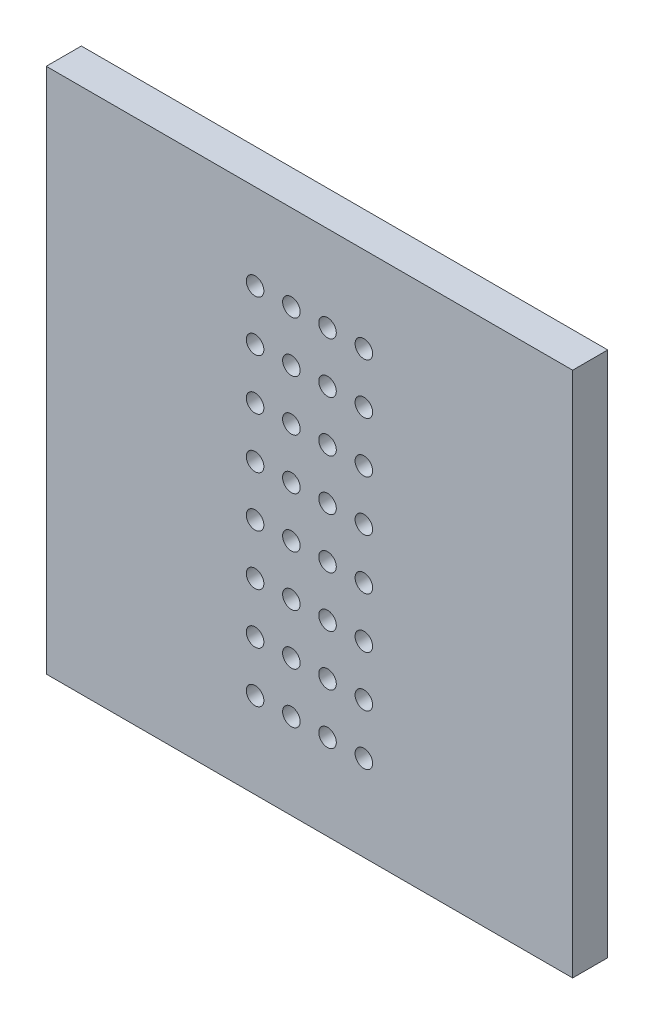
SolidWorks part; units mm, degrees
ref_plane "Plan de face" through (0, 0, 0) normal (0, 0, 1) x (1, 0, 0)
ref_plane "Plan de dessus" through (0, 0, 0) normal (0, 1, 0) x (1, 0, 0)
ref_plane "Plan de droite" through (0, 0, 0) normal (1, 0, 0) x (0, 0, -1)
sketch "Esquisse1" plane through (0, 0, 0) normal (0, 0, 1) x (1, 0, 0)
  line L1 (-15, -15) -> (15, -15)
  line L2 (-15, -15) -> (-15, 15)
  line L3 (-15, 15) -> (15, 15)
  line L4 (15, -15) -> (15, 15)
  line L5 (-15, -15) -> (15, 15) construction
  line L6 (-15, 15) -> (15, -15) construction
  point P0 (0, 0)
extrude "Base_Plate" add sketch "Esquisse1" along normal blind 2
sketch "Sketch_Perforations" plane through (0, 0, 2) normal (0, 0, 1) x (1, 0, 0)
  circle A0 centre (-3.1, -10.11) radius 0.5
  circle A1 centre (-3.1, -7.22) radius 0.5
  circle A2 centre (-3.1, -4.33) radius 0.5
  circle A3 centre (-3.1, -1.44) radius 0.5
  circle A4 centre (-3.1, 1.44) radius 0.5
  circle A5 centre (-3.1, 4.33) radius 0.5
  circle A6 centre (-3.1, 7.22) radius 0.5
  circle A7 centre (-3.1, 10.11) radius 0.5
  circle A8 centre (-1.03, -10.11) radius 0.5
  circle A9 centre (-1.03, -7.22) radius 0.5
  circle A10 centre (-1.03, -4.33) radius 0.5
  circle A11 centre (-1.03, -1.44) radius 0.5
  circle A12 centre (-1.03, 1.44) radius 0.5
  circle A13 centre (-1.03, 4.33) radius 0.5
  circle A14 centre (-1.03, 7.22) radius 0.5
  circle A15 centre (-1.03, 10.11) radius 0.5
  circle A16 centre (1.03, -10.11) radius 0.5
  circle A17 centre (1.03, -7.22) radius 0.5
  circle A18 centre (1.03, -4.33) radius 0.5
  circle A19 centre (1.03, -1.44) radius 0.5
  circle A20 centre (1.03, 1.44) radius 0.5
  circle A21 centre (1.03, 4.33) radius 0.5
  circle A22 centre (1.03, 7.22) radius 0.5
  circle A23 centre (1.03, 10.11) radius 0.5
  circle A24 centre (3.1, -10.11) radius 0.5
  circle A25 centre (3.1, -7.22) radius 0.5
  circle A26 centre (3.1, -4.33) radius 0.5
  circle A27 centre (3.1, -1.44) radius 0.5
  circle A28 centre (3.1, 1.44) radius 0.5
  circle A29 centre (3.1, 4.33) radius 0.5
  circle A30 centre (3.1, 7.22) radius 0.5
  circle A31 centre (3.1, 10.11) radius 0.5
extrude "Cut_Perforations" cut sketch "Sketch_Perforations" against normal blind 10
